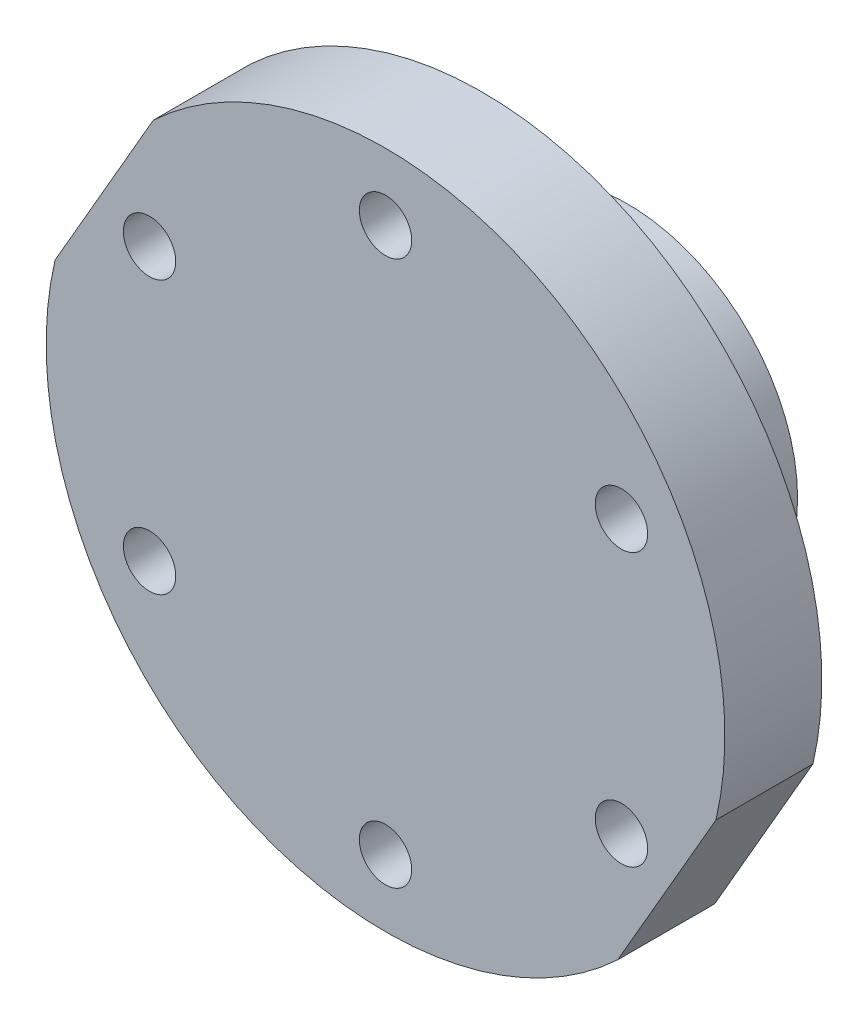
SolidWorks part; units mm, degrees
ref_plane "Front Plane" through (0, 0, 0) normal (0, 0, 1) x (1, 0, 0)
ref_plane "Top Plane" through (0, 0, 0) normal (0, 1, 0) x (1, 0, 0)
ref_plane "Right Plane" through (0, 0, 0) normal (1, 0, 0) x (0, 0, -1)
sketch "Sketch1" plane through (0, 0, 0) normal (0, 0, 1) x (1, 0, 0)
  circle A0 centre (0, 0) radius 28.1
  circle A1 centre (0, 28.1) radius 2.7
  circle A2 centre (24.3353, 14.05) radius 2.7
  circle A3 centre (24.3353, -14.05) radius 2.7
  circle A4 centre (0, -28.1) radius 2.7
  circle A5 centre (-24.3353, -14.05) radius 2.7
  circle A6 centre (-24.3353, 14.05) radius 2.7
  point P18 (0, 0)
  dimension "D1" = 56.2
  dimension "D2" = 5.4
  dimension "D3" = 6
sketch "Sketch3" plane through (0, 0, 0) normal (0, 0, 1) x (1, 0, 0)
  circle A0 centre (0, 0) radius 35
  circle A13 centre (0, 0) radius 6.15
  dimension "D1" = 70
  dimension "D2" = 12.3
extrude "Boss-Extrude1" add sketch "Sketch3" against normal blind 10
sketch "Sketch4" plane through (0, 0, -10) normal (0, 0, -1) x (-1, 0, 0)
  circle A0 centre (0, 0) radius 17.5
  circle A1 centre (0, 0) radius 6.15
  circle A2 centre (0, 0) radius 6.15 construction
  dimension "D2" = 35
extrude "Boss-Extrude2" add sketch "Sketch4" along normal blind 15
sketch "Sketch5" plane through (0, 0, 0) normal (0, 0, 1) x (1, 0, 0)
  circle A0 centre (0, 0) radius 6.15 construction
  circle A1 centre (0, 0) radius 6.15
extrude "Boss-Extrude3" add sketch "Sketch5" against normal blind 3
sketch "Sketch7" plane through (0, 0, 0) normal (0, 0, 1) x (1, 0, 0)
  circle A0 centre (-24.3353, 14.05) radius 2.7 construction
  circle A1 centre (-24.3353, -14.05) radius 2.7 construction
  circle A2 centre (0, -28.1) radius 2.7 construction
  circle A3 centre (24.3353, -14.05) radius 2.7 construction
  circle A4 centre (24.3353, 14.05) radius 2.7 construction
  circle A5 centre (0, 28.1) radius 2.7 construction
  circle A30 centre (-24.3353, 14.05) radius 2.7 construction
  circle A31 centre (-24.3353, -14.05) radius 2.7 construction
  circle A32 centre (0, -28.1) radius 2.7 construction
  circle A33 centre (24.3353, -14.05) radius 2.7 construction
  circle A34 centre (24.3353, 14.05) radius 2.7 construction
  circle A35 centre (0, 28.1) radius 2.7 construction
  circle A36 centre (-24.3353, 14.05) radius 2.7
  circle A37 centre (-24.3353, -14.05) radius 2.7
  circle A38 centre (0, -28.1) radius 2.7
  circle A39 centre (24.3353, -14.05) radius 2.7
  circle A40 centre (24.3353, 14.05) radius 2.7
  circle A41 centre (0, 28.1) radius 2.7
  dimension "D1" = 5.4
extrude "Cut-Extrude1" cut sketch "Sketch7" against normal blind 6
sketch "Sketch8" plane through (0, 0, 0) normal (0, 0, 1) x (1, 0, 0)
  line L0 (0, 0) -> (17.5, 30.3109) construction
  line L1 (-23.9436, 25.5285) -> (-34.0801, 7.9715)
  line L2 (34.0801, -7.9715) -> (23.9436, -25.5285)
  line L3 (0, 28.1) -> (24.3353, 14.05) construction
  circle A0 centre (0, 0) radius 35 construction
  arc A1 (-23.9436, 25.5285) -> (-34.0801, 7.9715) centre (0, 0) ccw
  arc A2 (23.9436, -25.5285) -> (34.0801, -7.9715) centre (0, 0) ccw
  point P10 (12.1677, 21.075)
  dimension "D1" = 67
extrude "Cut-Extrude2" cut sketch "Sketch8" against normal up to surface (10 mm away) up to face at (35, 0, -10)
ref_plane "Plane2" through (-29.0119, 16.75, -10) normal (0.5, 0.866, 0) x (0.866, -0.5, 0)
sketch "Sketch9" plane through (-29.0119, 16.75, -10) normal (0.5, 0.866, 0) x (0.866, -0.5, 0)
  line L0 (33.5, 15) -> (33.5, 0) construction
  line L1 (51, 15) -> (16, 15) construction
  line L2 (67, 0) -> (0, 0) construction
  circle A0 centre (33.5, 7.5) radius 1.65
  dimension "D1" = 3.3
extrude "Cut-Extrude3" cut sketch "Sketch9" against normal through all both and the other way through all
sketch "Sketch10" plane through (-29.0119, 16.75, -10) normal (0.5, 0.866, 0) x (0.866, -0.5, 0)
  line L1 (35.1743, 10.4) -> (31.8257, 10.4)
  line L2 (31.8257, 10.4) -> (30.1514, 7.5)
  line L3 (30.1514, 7.5) -> (31.8257, 4.6)
  line L4 (31.8257, 4.6) -> (35.1743, 4.6)
  line L5 (35.1743, 4.6) -> (36.8486, 7.5)
  line L6 (36.8486, 7.5) -> (35.1743, 10.4)
  circle A0 centre (33.5, 7.5) radius 2.9 construction
  dimension "D1" = 5.8
extrude "Cut-Extrude4" cut sketch "Sketch10" against normal mid plane 17.5
sketch "Sketch11" plane through (-29.0119, 16.75, -10) normal (0.5, 0.866, 0) x (0.866, -0.5, 0)
  circle A0 centre (33.5, 7.5) radius 2.8
  dimension "D1" = 5.6
extrude "Cut-Extrude5" cut sketch "Sketch11" against normal blind 5 from offset 20
mirror "Mirror1" about plane through (-29.0119, 16.75, -10) normal (0.5, 0.866, 0) of "Cut-Extrude5"
sketch "Sketch17" plane through (0, 0, -10) normal (0, 0, -1) x (-1, 0, 0)
  line L0 (0, 0) -> (29.0119, 16.75) construction
  line L1 (23.9436, 25.5285) -> (34.0801, 7.9715) construction
  line L2 (0, 28.1) -> (24.3353, 14.05) construction
  line L3 (0, 0) -> (14.05, 24.3353) construction
  line L4 (0, 0) -> (-17.5, 30.3109) construction
  circle A0 centre (14.05, 24.3353) radius 2.1
  circle A1 centre (28.1, 0) radius 2.1
  circle A2 centre (0, 0) radius 28.1 construction
  arc A3 (23.9436, 25.5285) -> (-34.0801, -7.9715) centre (0, 0) ccw construction
  circle A4 centre (-28.1, 0) radius 2.1
  circle A5 centre (-14.05, -24.3353) radius 2.1
  point P9 (12.1677, 21.075)
  dimension "D1" = 4.2
extrude "Cut-Extrude6" cut sketch "Sketch17" against normal blind 3.5
sketch "Sketch18" plane through (0, 0, -10) normal (0, 0, -1) x (-1, 0, 0)
  line L0 (26.6447, 18.05) -> (22.0259, 18.05)
  line L1 (-2.3094, 32.1) -> (-4.6188, 28.1)
  line L2 (-4.6188, 28.1) -> (-2.3094, 24.1)
  line L3 (-2.3094, 24.1) -> (2.3094, 24.1)
  line L4 (2.3094, 24.1) -> (4.6188, 28.1)
  line L5 (4.6188, 28.1) -> (2.3094, 32.1)
  line L6 (2.3094, 32.1) -> (-2.3094, 32.1)
  line L7 (22.0259, 18.05) -> (19.7165, 14.05)
  line L8 (19.7165, 14.05) -> (22.0259, 10.05)
  line L9 (22.0259, 10.05) -> (26.6447, 10.05)
  line L10 (26.6447, 10.05) -> (28.9541, 14.05)
  line L11 (28.9541, 14.05) -> (26.6447, 18.05)
  line L12 (28.9541, -14.05) -> (26.6447, -10.05)
  line L13 (26.6447, -10.05) -> (22.0259, -10.05)
  line L14 (22.0259, -10.05) -> (19.7165, -14.05)
  line L15 (19.7165, -14.05) -> (22.0259, -18.05)
  line L16 (22.0259, -18.05) -> (26.6447, -18.05)
  line L17 (26.6447, -18.05) -> (28.9541, -14.05)
  line L18 (2.3094, -32.1) -> (4.6188, -28.1)
  line L19 (4.6188, -28.1) -> (2.3094, -24.1)
  line L20 (2.3094, -24.1) -> (-2.3094, -24.1)
  line L21 (-2.3094, -24.1) -> (-4.6188, -28.1)
  line L22 (-4.6188, -28.1) -> (-2.3094, -32.1)
  line L23 (-2.3094, -32.1) -> (2.3094, -32.1)
  line L24 (-26.6447, -18.05) -> (-22.0259, -18.05)
  line L25 (-22.0259, -18.05) -> (-19.7165, -14.05)
  line L26 (-19.7165, -14.05) -> (-22.0259, -10.05)
  line L27 (-22.0259, -10.05) -> (-26.6447, -10.05)
  line L28 (-26.6447, -10.05) -> (-28.9541, -14.05)
  line L29 (-28.9541, -14.05) -> (-26.6447, -18.05)
  line L30 (-28.9541, 14.05) -> (-26.6447, 10.05)
  line L31 (-26.6447, 10.05) -> (-22.0259, 10.05)
  line L32 (-22.0259, 10.05) -> (-19.7165, 14.05)
  line L33 (-19.7165, 14.05) -> (-22.0259, 18.05)
  line L34 (-22.0259, 18.05) -> (-26.6447, 18.05)
  line L35 (-26.6447, 18.05) -> (-28.9541, 14.05)
  line L36 (22.0259, 18.05) -> (26.6447, 10.05) construction
  circle A0 centre (0, 28.1) radius 4 construction
  circle A1 centre (24.3353, 14.05) radius 2.7 construction
  point P1 (24.3353, 14.05)
  point P42 (0, 0)
  point P43 (21.6788, 18.2398)
  dimension "D1" = 8
  dimension "D2" = 6
extrude "Cut-Extrude7" cut sketch "Sketch18" against normal blind 4
